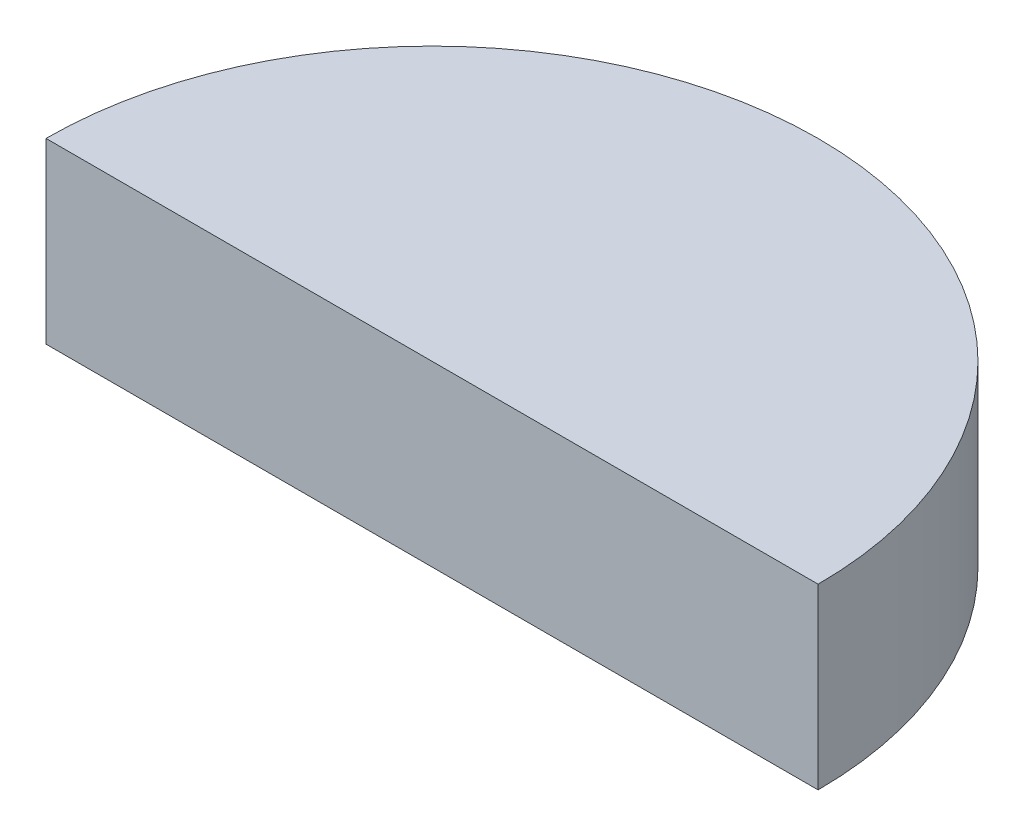
SolidWorks part; units mm, degrees
ref_plane "Front Plane" through (0, 0, 0) normal (0, 0, 1) x (1, 0, 0)
ref_plane "Top Plane" through (0, 0, 0) normal (0, 1, 0) x (1, 0, 0)
ref_plane "Right Plane" through (0, 0, 0) normal (1, 0, 0) x (0, 0, -1)
sketch "Sketch1" plane through (0, 0, 0) normal (0, 1, 0) x (1, 0, 0)
  line L0 (-13, 0) -> (-9, 0)
  line L1 (9, 0) -> (13, 0)
  circle A0 centre (0, 0) radius 12.43 construction
  circle A1 centre (0, 0) radius 9.43 construction
  circle A2 centre (0, 0) radius 13 construction
  circle A3 centre (0, 0) radius 9 construction
  arc A4 (9, 0) -> (-9, 0) centre (0, 0) ccw
  arc A5 (13, 0) -> (-13, 0) centre (0, 0) ccw
  dimension "D1" = 18.86
  dimension "D2" = 24.86
  dimension "D3" = 26
  dimension "D4" = 18
sketch "Sketch2" plane through (0, 0, 0) normal (0, 1, 0) x (1, 0, 0)
  line L0 (-13, 0) -> (13, 0)
  arc A0 (13, 0) -> (-13, 0) centre (0, 0) ccw construction
  arc A1 (13, 0) -> (-13, 0) centre (0, 0) ccw
extrude "Boss-Extrude1" add sketch "Sketch2" along normal blind 6
